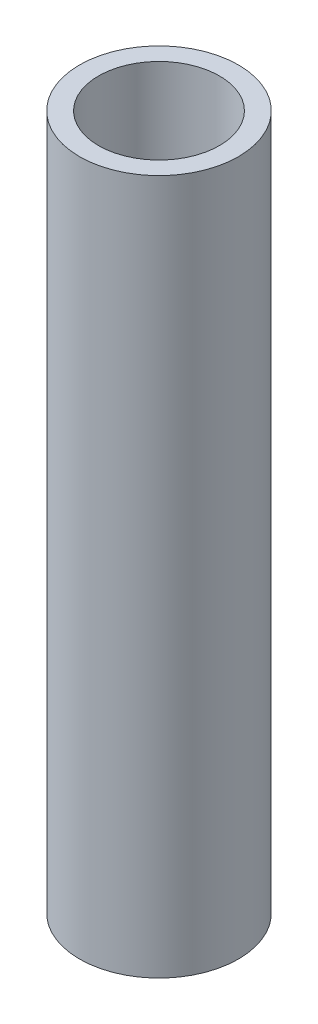
SolidWorks part; units mm, degrees
material "PVC 0.007 Plasticized"
ref_plane "Front Plane" through (0, 0, 0) normal (0, 0, 1) x (1, 0, 0)
ref_plane "Top Plane" through (0, 0, 0) normal (0, 1, 0) x (1, 0, 0)
ref_plane "Right Plane" through (0, 0, 0) normal (1, 0, 0) x (0, 0, -1)
sketch "Sketch1" plane through (0, 0, 0) normal (0, 1, 0) x (1, 0, 0)
  circle A0 centre (0, 0) radius 12.7
  circle A1 centre (0, 0) radius 16.7005
  dimension "D1" = 25.4
  dimension "D2" = 33.401
extrude "Boss-Extrude1" add sketch "Sketch1" along normal blind 146.05 contours A1 A0
